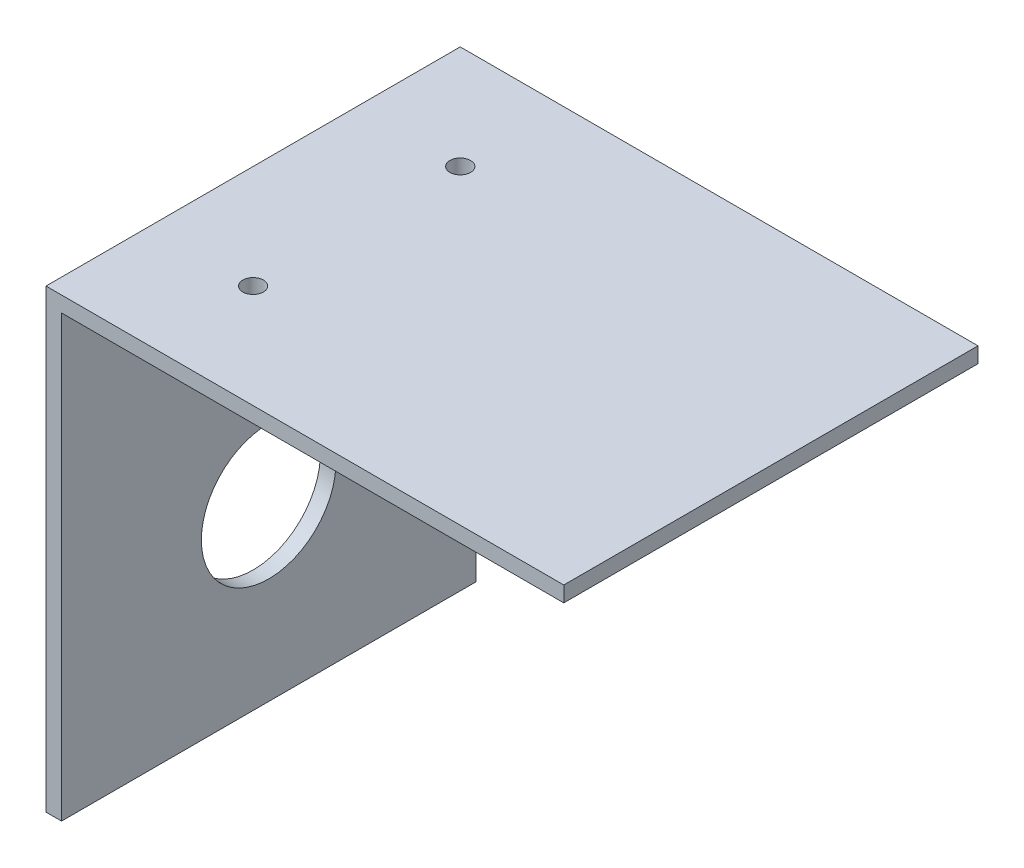
SolidWorks part; units mm, degrees
ref_plane "Front Plane" through (0, 0, 0) normal (0, 0, 1) x (1, 0, 0)
ref_plane "Top Plane" through (0, 0, 0) normal (0, 1, 0) x (1, 0, 0)
ref_plane "Right Plane" through (0, 0, 0) normal (1, 0, 0) x (0, 0, -1)
sketch "Sketch2" plane through (0, 0, 0) normal (0, 1, 0) x (1, 0, 0)
  line L1 (-50, -40) -> (50, -40)
  line L2 (-50, -40) -> (-50, 40)
  line L3 (-50, 40) -> (50, 40)
  line L4 (50, -40) -> (50, 40)
  line L5 (-50, -40) -> (50, 40) construction
  line L6 (-50, 40) -> (50, -40) construction
  point P0 (0, 0)
  dimension "D1" = 100
  dimension "D2" = 80
extrude "Boss-Extrude1" add sketch "Sketch2" along normal blind 3
sketch "Sketch3" plane through (0, 0, 0) normal (0, -1, 0) x (1, 0, 0)
  line L0 (50, -40) -> (-50, -40) construction
  line L1 (-50, 40) -> (-47, 40)
  line L2 (-50, 40) -> (-50, -40)
  line L3 (-50, -40) -> (-47, -40)
  line L4 (-47, 40) -> (-47, -40)
  dimension "D1" = 80
  dimension "D2" = 3
extrude "Boss-Extrude2" add sketch "Sketch3" along normal blind 100
sketch "Sketch6" plane through (-50, 0, 0) normal (-1, 0, 0) x (0, 0, 1)
  line L0 (0, 3) -> (0, -100) construction
  line L1 (-40, 3) -> (40, 3) construction
  line L3 (40, -100) -> (-40, -100) construction
  circle A0 centre (0, -51.5) radius 13
  point P9 (0, -48.5)
  dimension "D2" = 26
  dimension "D1" = 3
sketch "Sketch8" plane through (0, 3, 0) normal (0, 1, 0) x (1, 0, 0)
  line L3 (50, 40) -> (-50, 40) construction
  line L4 (-50, 40) -> (-50, -40) construction
  line L5 (-50, -40) -> (50, -40) construction
  circle A0 centre (-30, 20) radius 2
  circle A1 centre (-30, -20) radius 2
  dimension "D3" = 20
  dimension "D4" = 20
  dimension "D1" = 4
  dimension "D2" = 4
  dimension "D5" = 20
  dimension "D6" = 20
extrude "Cut-Extrude3" cut sketch "Sketch8" against normal blind 61
extrude "Cut-Extrude4" cut sketch "Sketch6" against normal blind 10 contours A0
sketch "Sketch9" plane through (0, -100, 0) normal (0, -1, 0) x (1, 0, 0)
  line L1 (-50, 40) -> (-47, 40)
  line L2 (-50, 40) -> (-50, -40)
  line L3 (-50, -40) -> (-47, -40)
  line L4 (-47, 40) -> (-47, -40)
extrude "Cut-Extrude5" cut sketch "Sketch9" against normal blind 15
